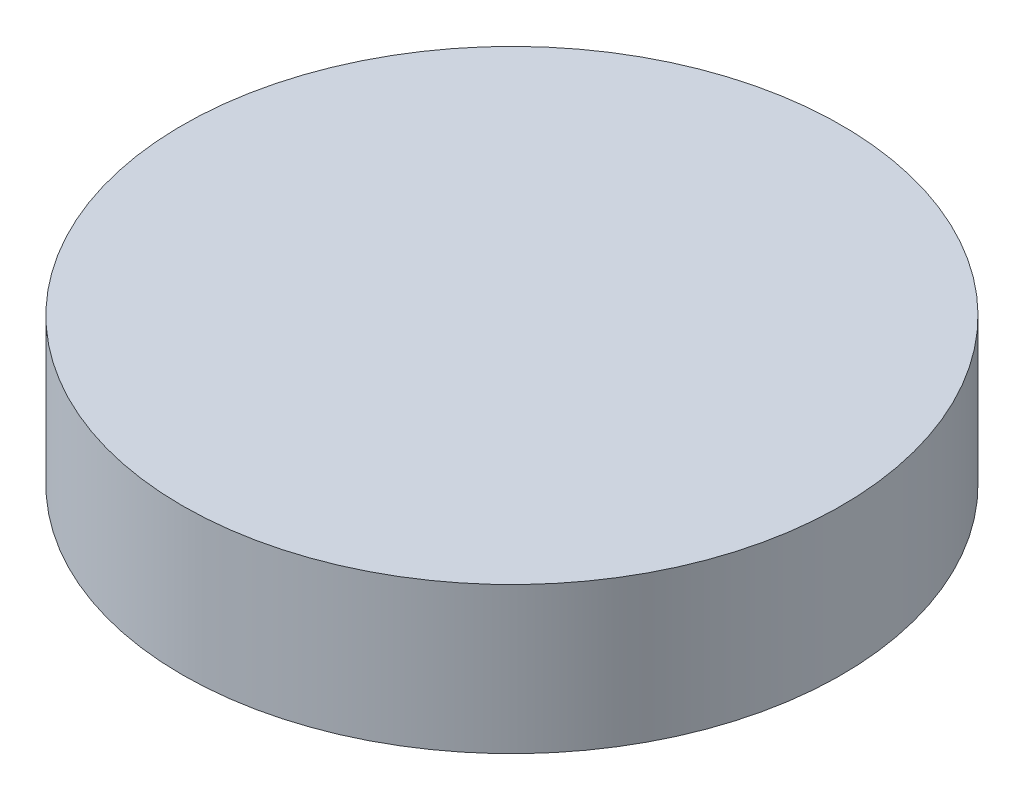
SolidWorks part; units mm, degrees
ref_plane "Front Plane" through (0, 0, 0) normal (0, 0, 1) x (1, 0, 0)
ref_plane "Top Plane" through (0, 0, 0) normal (0, 1, 0) x (1, 0, 0)
ref_plane "Right Plane" through (0, 0, 0) normal (1, 0, 0) x (0, 0, -1)
sketch "Sketch1" plane through (0, 0, 0) normal (0, 1, 0) x (1, 0, 0)
  circle A0 centre (0, 0) radius 45
  dimension "D1" = 90
extrude "Boss-Extrude1" add sketch "Sketch1" along normal blind 20
